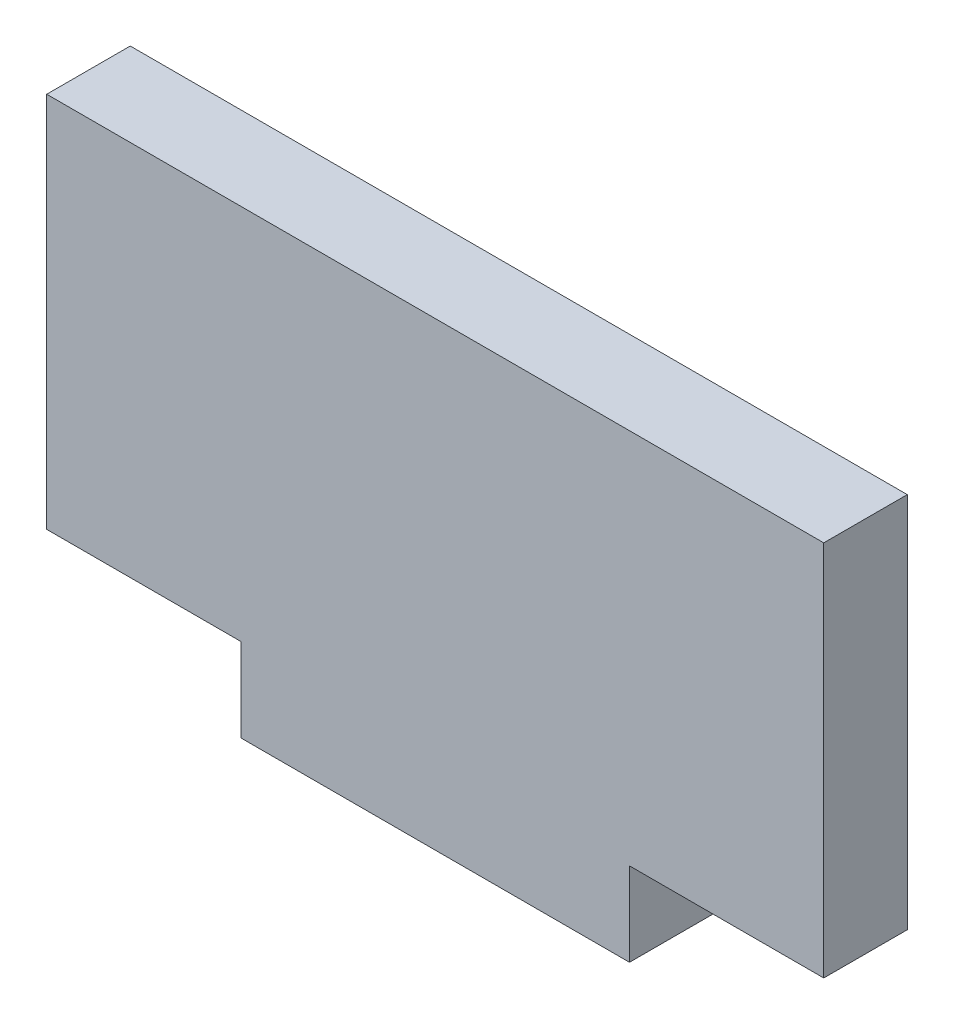
SolidWorks part; units mm, degrees
ref_plane "Front Plane" through (0, 0, 0) normal (0, 0, 1) x (1, 0, 0)
ref_plane "Top Plane" through (0, 0, 0) normal (0, 1, 0) x (1, 0, 0)
ref_plane "Right Plane" through (0, 0, 0) normal (1, 0, 0) x (0, 0, -1)
sketch "Sketch1" plane through (0, 0, 0) normal (0, 0, 1) x (1, 0, 0)
  line L1 (-12.7, 2.7305) -> (12.7, 2.7305)
  line L2 (-12.7, 2.7305) -> (-12.7, -2.7305)
  line L3 (-12.7, -2.7305) -> (12.7, -2.7305)
  line L4 (12.7, 2.7305) -> (12.7, -2.7305)
  line L5 (-12.7, 2.7305) -> (12.7, -2.7305) construction
  line L6 (-12.7, -2.7305) -> (12.7, 2.7305) construction
  line L7 (-25.4, 27.3685) -> (25.4, 27.3685)
  line L8 (-25.4, 27.3685) -> (-25.4, 2.7305)
  line L9 (-25.4, 2.7305) -> (25.4, 2.7305)
  line L10 (25.4, 27.3685) -> (25.4, 2.7305)
  line L11 (-25.4, 27.3685) -> (25.4, 2.7305) construction
  line L12 (-25.4, 2.7305) -> (25.4, 27.3685) construction
  point P0 (0, 0)
  point P6 (0, 15.0495)
  point P11 (0, 0)
  dimension "D1" = 5.461
  dimension "D2" = 25.4
  dimension "D3" = 50.8
  dimension "D4" = 24.638
extrude "Boss-Extrude1" add sketch "Sketch1" along normal blind 5.461 contours L10 L7 L8 L9 L1 | L4 L1 L2 L3
